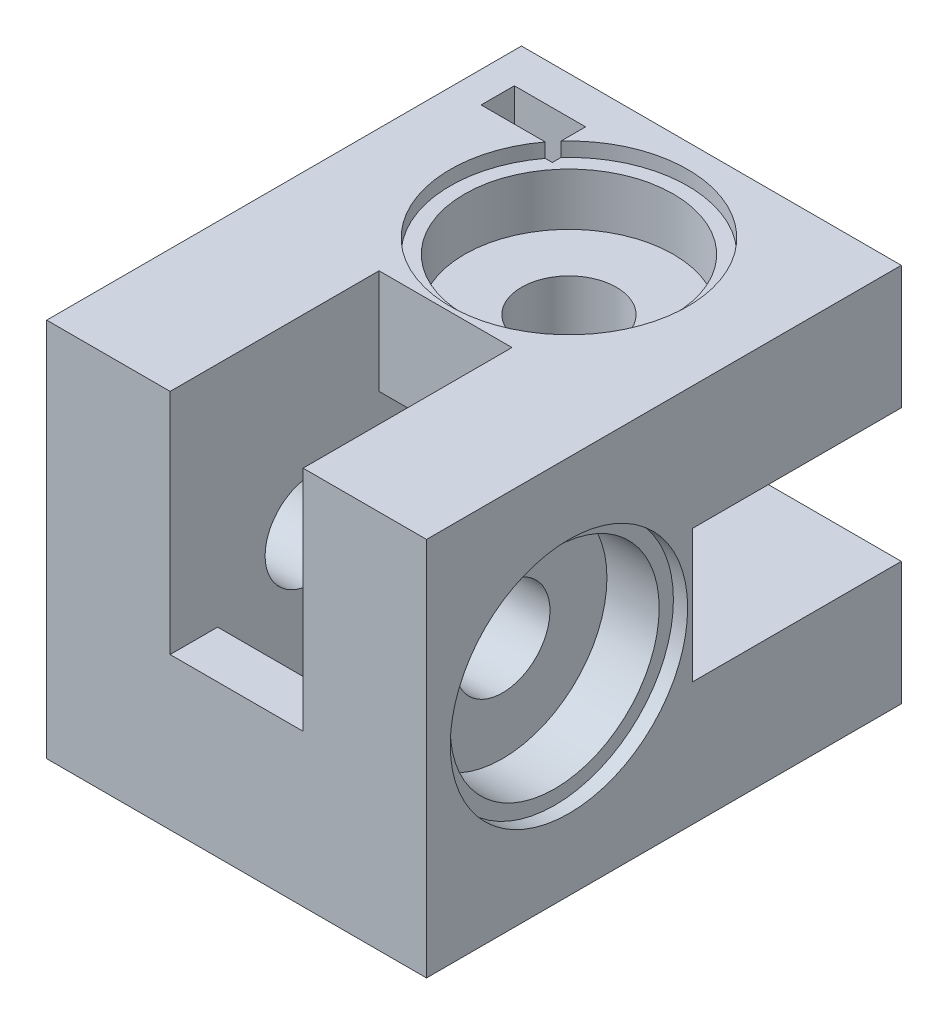
SolidWorks part; units mm, degrees
ref_plane "Plan de face" through (0, 0, 0) normal (0, 0, 1) x (1, 0, 0)
ref_plane "Plan de dessus" through (0, 0, 0) normal (0, 1, 0) x (1, 0, 0)
ref_plane "Plan de droite" through (0, 0, 0) normal (1, 0, 0) x (0, 0, -1)
sketch "Esquisse1" plane through (0, 0, 0) normal (0, 0, 1) x (1, 0, 0)
  line L1 (-40, 40) -> (0, 40)
  line L2 (-40, 40) -> (-40, 0)
  line L3 (-40, 0) -> (0, 0)
  line L4 (0, 40) -> (0, 0)
  dimension "D1" = 40
  dimension "D2" = 40
extrude "Boss.-Extru.1" add sketch "Esquisse1" along normal blind 50
sketch "Esquisse2" plane through (0, 40, 0) normal (0, 1, 0) x (1, 0, 0)
  line L0 (0, 0) -> (-40, 0) construction
  line L1 (-40, -50) -> (-40, 0) construction
  circle A0 centre (-20, -15) radius 5
  dimension "D1" = 10
  dimension "D2" = 15
  dimension "D3" = 20
extrude "Enlèv. mat.-Extru.1" cut sketch "Esquisse2" against normal through all
sketch "Esquisse3" plane through (-40, 0, 0) normal (-1, 0, 0) x (0, 0, 1)
  line L0 (50, 40) -> (50, 0) construction
  line L1 (50, 40) -> (0, 40) construction
  circle A0 centre (35, 20) radius 5
  dimension "D1" = 10
  dimension "D2" = 15
  dimension "D3" = 20
extrude "Enlèv. mat.-Extru.2" cut sketch "Esquisse3" against normal through all
sketch "Esquisse4" plane through (-40, 0, 0) normal (-1, 0, 0) x (0, 0, 1)
  line L1 (25, 27) -> (5, 27)
  line L2 (25, 27) -> (25, 13)
  line L3 (25, 13) -> (5, 13)
  line L4 (5, 27) -> (5, 13)
  line L5 (0, 40) -> (0, 0) construction
  line L6 (50, 0) -> (0, 0) construction
  line L7 (50, 40) -> (0, 40) construction
  dimension "D1" = 14
  dimension "D2" = 20
  dimension "D3" = 5
  dimension "D4" = 13
  dimension "D5" = 13
extrude "Enlèv. mat.-Extru.3" cut sketch "Esquisse4" against normal blind 29
sketch "Esquisse5" plane through (0, 0, 0) normal (0, -1, 0) x (1, 0, 0)
  line L0 (-40, 50) -> (0, 50) construction
  line L1 (-13, 25) -> (-27, 25)
  line L2 (-13, 25) -> (-13, 45)
  line L3 (-13, 45) -> (-27, 45)
  line L4 (-27, 25) -> (-27, 45)
  line L5 (-40, 50) -> (-40, 0) construction
  dimension "D1" = 20
  dimension "D2" = 5
  dimension "D3" = 14
  dimension "D4" = 13
extrude "Enlèv. mat.-Extru.4" cut sketch "Esquisse5" against normal blind 29
sketch "Esquisse6" plane through (0, 0, 0) normal (1, 0, 0) x (0, 0, -1)
  line L0 (0, 0) -> (0, 40) construction
  line L1 (0, 27) -> (-22, 27)
  line L2 (0, 27) -> (0, 13)
  line L3 (0, 13) -> (-22, 13)
  line L4 (-22, 27) -> (-22, 13)
  line L5 (-50, 0) -> (0, 0) construction
  dimension "D1" = 14
  dimension "D2" = 22
  dimension "D3" = 13
extrude "Enlèv. mat.-Extru.5" cut sketch "Esquisse6" against normal blind 24
sketch "Esquisse7" plane through (0, 40, 0) normal (0, 1, 0) x (1, 0, 0)
  line L0 (0, -50) -> (-40, -50) construction
  line L1 (-27, -50) -> (-13, -50)
  line L2 (-27, -50) -> (-27, -28)
  line L3 (-27, -28) -> (-13, -28)
  line L4 (-13, -50) -> (-13, -28)
  line L5 (-40, -50) -> (-40, 0) construction
  dimension "D1" = 14
  dimension "D2" = 22
  dimension "D3" = 13
extrude "Enlèv. mat.-Extru.6" cut sketch "Esquisse7" against normal blind 24
sketch "Esquisse8" plane through (0, 0, 0) normal (1, 0, 0) x (0, 0, -1)
  circle A0 centre (-35, 20) radius 11
  dimension "D1" = 22
extrude "Enlèv. mat.-Extru.7" cut sketch "Esquisse8" against normal blind 7
sketch "Esquisse9" plane through (0, 0, 0) normal (1, 0, 0) x (0, 0, -1)
  circle A0 centre (-35, 20) radius 12.5
  dimension "D1" = 25
extrude "Enlèv. mat.-Extru.8" cut sketch "Esquisse9" against normal blind 1.5
sketch "Esquisse10" plane through (0, 40, 0) normal (0, 1, 0) x (1, 0, 0)
  circle A0 centre (-20, -15) radius 11
  dimension "D1" = 22
extrude "Enlèv. mat.-Extru.9" cut sketch "Esquisse10" against normal blind 7
sketch "Esquisse11" plane through (0, 40, 0) normal (0, 1, 0) x (1, 0, 0)
  circle A0 centre (-20, -15) radius 12.5
  dimension "D1" = 25
extrude "Enlèv. mat.-Extru.10" cut sketch "Esquisse11" against normal blind 1.5
sketch "Esquisse13" plane through (0, 0, 0) normal (0, 0, -1) x (-1, 0, 0)
  line L0 (-3.8974, 32) -> (45.9898, 32) construction
  line L1 (8, 41.5021) -> (8, -1.9426) construction
  line L2 (0, 27) -> (0, 40) construction
  line L4 (0, 40) -> (40, 40) construction
  line L8 (0, 0) -> (0, 13) construction
  line L9 (28, 0) -> (0, 0) construction
  line L10 (40, 40) -> (40, 12) construction
  circle A0 centre (33, 32) radius 2.2
  circle A1 centre (8, 7) radius 2.2
  dimension "D1" = 7
  dimension "D2" = 7
  dimension "D3" = 33
  dimension "D4" = 33
  dimension "D5" = 8
  dimension "D6" = 8
extrude "Enlèv. mat.-Extru.11" cut sketch "Esquisse13" against normal blind 10
sketch "Esquisse15" plane through (0, 40, 0) normal (0, 1, 0) x (1, 0, 0)
  line L0 (-40, -50) -> (-40, 0) construction
  line L1 (-36.75, -4) -> (-29.25, -4)
  line L2 (-36.75, -4) -> (-36.75, -7.5)
  line L3 (-36.75, -7.5) -> (-29.25, -7.5)
  line L4 (-29.25, -4) -> (-29.25, -7.5)
  line L5 (-36.75, -4) -> (-29.25, -7.5) construction
  line L6 (-36.75, -7.5) -> (-29.25, -4) construction
  line L9 (0, 0) -> (-40, 0) construction
  point P0 (-33, -5.75)
  point P9 (-35.0503, 0)
  dimension "D1" = 7
  dimension "D2" = 4
extrude "Enlèv. mat.-Extru.13" cut sketch "Esquisse15" against normal blind 12
sketch "Esquisse16" plane through (0, 0, 0) normal (0, -1, 0) x (1, 0, 0)
  line L0 (-40, 0) -> (0, 0) construction
  line L1 (-4.25, 4) -> (-11.75, 4)
  line L2 (-4.25, 4) -> (-4.25, 7.5)
  line L3 (-4.25, 7.5) -> (-11.75, 7.5)
  line L4 (-11.75, 4) -> (-11.75, 7.5)
  line L5 (-4.25, 4) -> (-11.75, 7.5) construction
  line L6 (-4.25, 7.5) -> (-11.75, 4) construction
  line L7 (0, 50) -> (0, 0) construction
  point P0 (-8, 5.75)
  dimension "D1" = 4
  dimension "D2" = 8
extrude "Enlèv. mat.-Extru.14" cut sketch "Esquisse16" against normal blind 12
